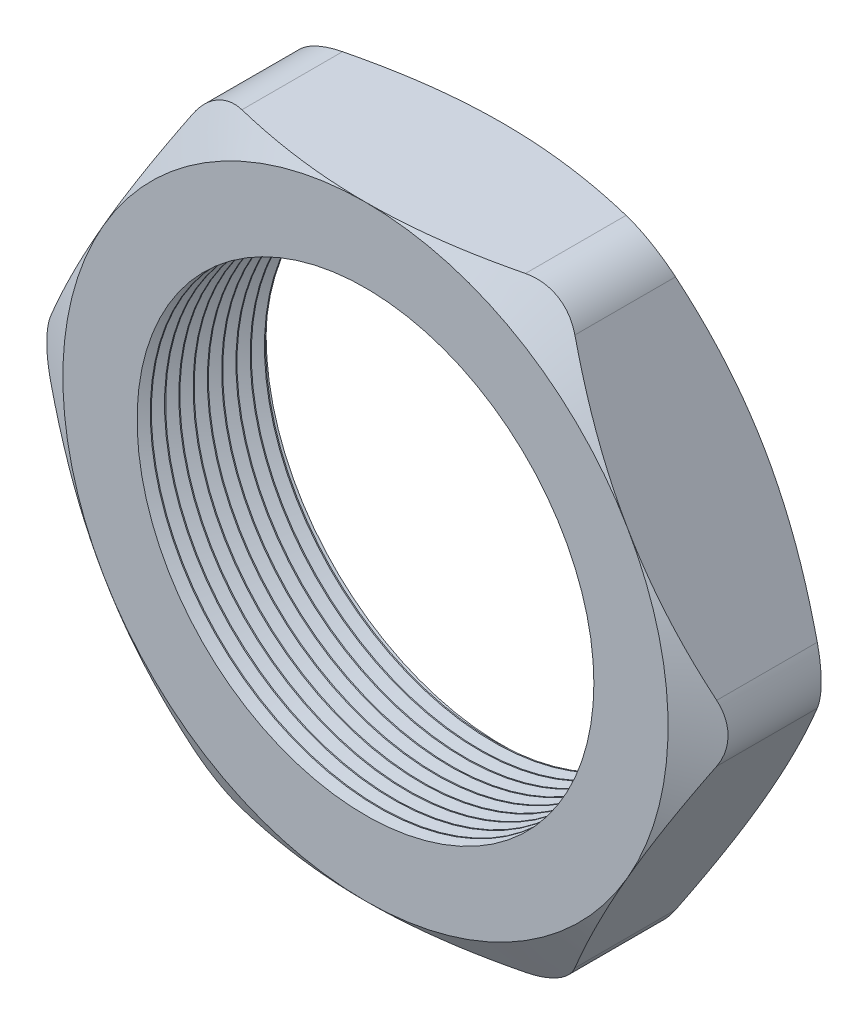
SolidWorks part; units mm, degrees
ref_plane "Front Plane" through (0, 0, 0) normal (0, 0, 1) x (1, 0, 0)
ref_plane "Top Plane" through (0, 0, 0) normal (0, 1, 0) x (1, 0, 0)
ref_plane "Right Plane" through (0, 0, 0) normal (1, 0, 0) x (0, 0, -1)
sketch "Sketch1" plane through (0, 0, 0) normal (0, 0, 1) x (1, 0, 0)
  line L1 (-15.5446, 0) -> (-7.7723, -13.462)
  line L2 (-7.7723, -13.462) -> (7.7723, -13.462)
  line L3 (7.7723, -13.462) -> (15.5446, 0)
  line L4 (15.5446, 0) -> (7.7723, 13.462)
  line L5 (7.7723, 13.462) -> (-7.7723, 13.462)
  line L6 (-7.7723, 13.462) -> (-15.5446, 0)
  circle A0 centre (0, 0) radius 13.462 construction
  circle A1 centre (0, 0) radius 10.16
  dimension "TS" = 20.32
  dimension "H" = 26.924
extrude "Extrude1" add sketch "Sketch1" along normal blind 6.096
sketch "Sketch2" plane through (0, 0, 6.096) normal (0, 0, 1) x (1, 0, 0)
  line L0 (7.7723, 13.462) -> (-7.7723, 13.462) construction
  circle A0 centre (0, 0) radius 13.462
extrude "Cut-Extrude1" cut sketch "Sketch2" against normal through all draft 60 flip side to cut
sketch "Sketch3" plane through (0, 0, 0) normal (0, 0, -1) x (-1, 0, 0)
  line L0 (-7.7723, 13.462) -> (7.7723, 13.462) construction
  circle A0 centre (0, 0) radius 13.462
extrude "Cut-Extrude2" cut sketch "Sketch3" against normal through all draft 60 flip side to cut
fillet "Fillet1" radius 2.54 6 edges at (15.5446, 0, 3.048) (7.7723, -13.462, 3.048) (-7.7723, -13.462, 3.048) (-15.5446, 0, 3.048) (-7.7723, 13.462, 3.048) (7.7723, 13.462, 3.048)
sketch "Sketch4" plane through (0, 0, 0) normal (0, 1, 0) x (1, 0, 0)
  line L0 (-10.16, -6.096) -> (-10.16, -5.5094)
  line L1 (-10.16, 0) -> (-10.16, -6.096) construction
  line L2 (-10.16, -5.5094) -> (-10.668, -5.8027)
  line L3 (-10.668, -5.8027) -> (-10.16, -6.096)
  dimension "D1" = 60
  dimension "D2" = 60
  dimension "D3" = 0.508
revolve "Cut-Revolve1" cut sketch "Sketch4" angle 360 about axis through (0, 0, 0) along (0, 0, 1)
pattern_linear "LPattern1" count 10 spacing 0.635 along (0, 0, -1) of "Cut-Revolve1"
